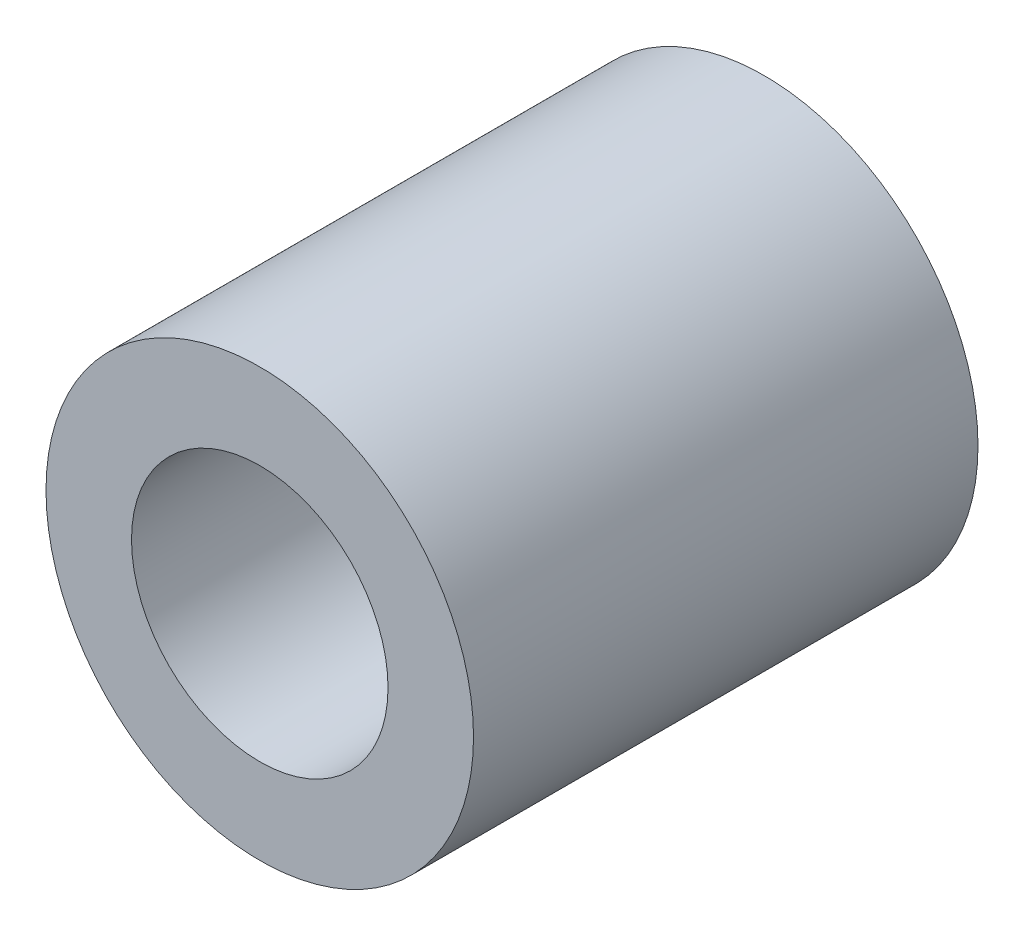
SolidWorks part; units mm, degrees
material "ﾎﾟﾘｵｷｼﾒﾁﾚﾝ(POM)ｱｾﾀｰﾙ共重合体"
ref_plane "Front Plane" through (0, 0, 0) normal (0, 0, 1) x (1, 0, 0)
ref_plane "Top Plane" through (0, 0, 0) normal (0, 1, 0) x (1, 0, 0)
ref_plane "Right Plane" through (0, 0, 0) normal (1, 0, 0) x (0, 0, -1)
sketch "Sketch2" plane through (0, 0, 0) normal (0, 0, 1) x (1, 0, 0)
  circle A0 centre (0, 0) radius 2.5
  circle A1 centre (0, 0) radius 1.5
  dimension "D1" = 3
  dimension "D2" = 5
  dimension "D3" = 5
extrude "Boss-Extrude1" add sketch "Sketch2" along normal blind 5.9
